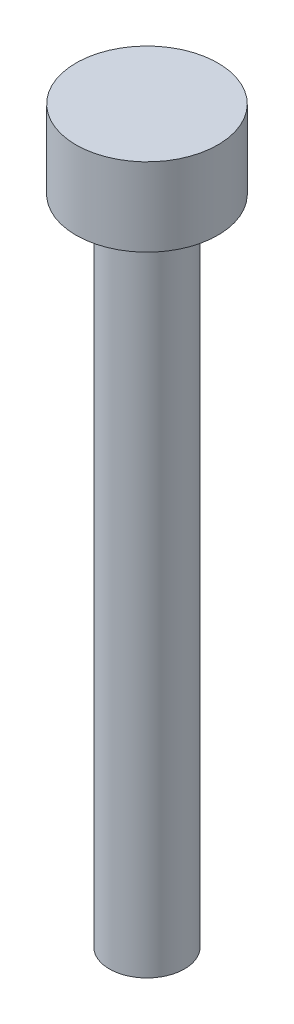
SolidWorks part; units mm, degrees
ref_plane "Front Plane" through (0, 0, 0) normal (0, 0, 1) x (1, 0, 0)
ref_plane "Top Plane" through (0, 0, 0) normal (0, 1, 0) x (1, 0, 0)
ref_plane "Right Plane" through (0, 0, 0) normal (1, 0, 0) x (0, 0, -1)
sketch "Sketch1" plane through (0, 0, 0) normal (0, 1, 0) x (1, 0, 0)
  circle A0 centre (0, 0) radius 2.72
  dimension "D1" = 5.44
extrude "Boss-Extrude1" add sketch "Sketch1" along normal blind 3
sketch "Sketch2" plane through (0, 0, 0) normal (0, -1, 0) x (1, 0, 0)
  circle A0 centre (0, 0) radius 1.44
  dimension "D1" = 2.88
extrude "Boss-Extrude2" add sketch "Sketch2" along normal blind 25
